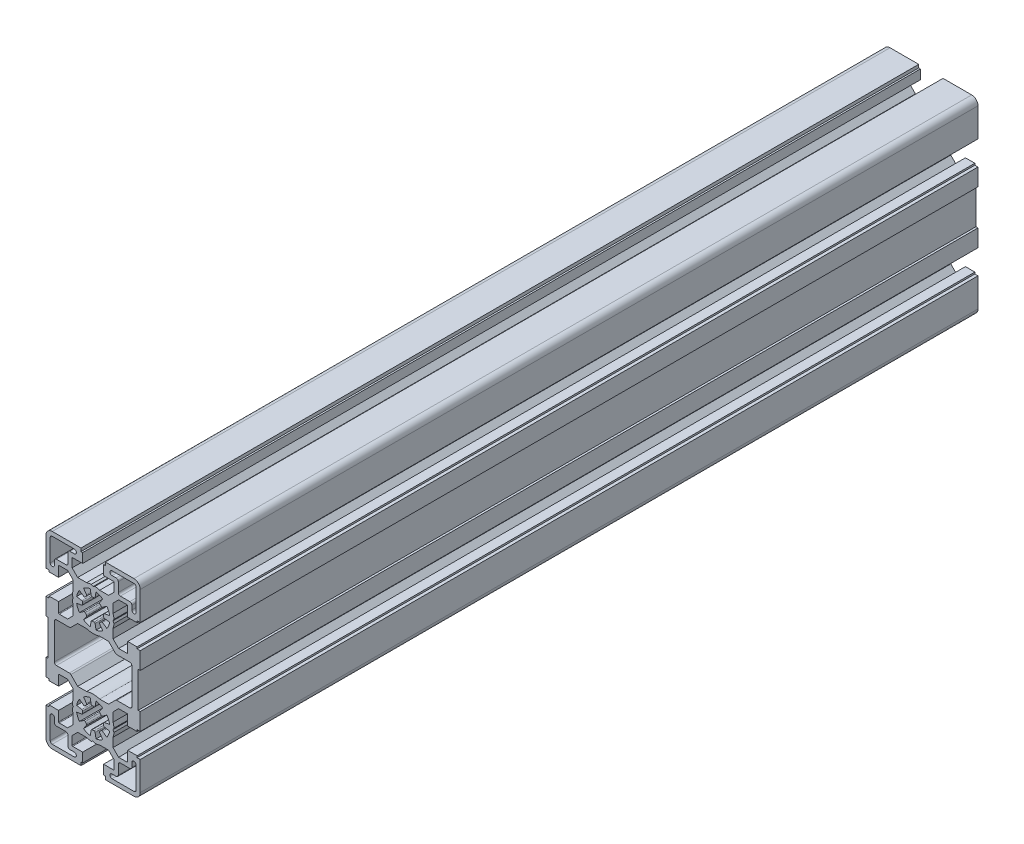
SolidWorks part; units mm, degrees
ref_plane "Спереди" through (0, 0, 0) normal (0, 0, 1) x (1, 0, 0)
ref_plane "Сверху" through (0, 0, 0) normal (0, 1, 0) x (1, 0, 0)
ref_plane "Справа" through (0, 0, 0) normal (1, 0, 0) x (0, 0, -1)
sketch "Эскиз1" plane through (0, 0, 0) normal (0, 0, 1) x (1, 0, 0)
  line L0 (-0.9511, 27.894) -> (-1.3892, 30.3785)
  line L1 (-3.1416, 26.9867) -> (-4.5886, 29.0532)
  line L2 (-4.4867, 25.6416) -> (-6.5532, 27.0886)
  line L3 (7.8785, 21.1108) -> (5.394, 21.5489)
  line L4 (-5.394, 23.4511) -> (-7.8785, 23.8892)
  line L5 (16.5, 27.5) -> (21, 27.5)
  line L6 (-21, 27.5) -> (-16.5, 27.5)
  line L7 (21, 28.3) -> (22.5, 28.3)
  line L8 (-22.5, 28.3) -> (-21, 28.3)
  line L9 (3.1225, 32) -> (7.3787, 32)
  line L10 (-7.3787, 32) -> (-3.1225, 32)
  line L11 (12.1713, 32.55) -> (16.2, 32.55)
  line L12 (-16.2, 32.55) -> (-12.1713, 32.55)
  line L13 (-17.5, 34.5) -> (-13, 34.5)
  line L14 (5, 39) -> (9.75, 39)
  line L15 (-9.75, 39) -> (-5, 39)
  line L16 (-19.5, 43) -> (-9, 43)
  line L17 (5, 43.5) -> (5.8, 43.5)
  line L18 (-5.8, 43.5) -> (-5, 43.5)
  line L19 (5.8, 45) -> (19.5, 45)
  line L20 (-19.5, 45) -> (-5.8, 45)
  line L21 (-7.8785, 21.1108) -> (-5.394, 21.5489)
  line L22 (5.394, 23.4511) -> (7.8785, 23.8892)
  line L23 (4.4867, 25.6416) -> (6.5532, 27.0886)
  line L24 (3.1416, 26.9867) -> (4.5886, 29.0532)
  line L25 (0.9511, 27.894) -> (1.3892, 30.3785)
  line L26 (-22.5, 28.3) -> (-22.5, 42)
  line L27 (-21, 27.5) -> (-21, 28.3)
  line L28 (-20.5, 31.5) -> (-20.5, 42)
  line L29 (-16.5, 27.5) -> (-16.5, 32.25)
  line L30 (-12, 35.5) -> (-12, 40)
  line L31 (-5.8, 43.5) -> (-5.8, 45)
  line L32 (-5, 39) -> (-5, 43.5)
  line L33 (5, 39) -> (5, 43.5)
  line L34 (5.8, 43.5) -> (5.8, 45)
  line L35 (9.5, 25.6225) -> (9.5, 29.8787)
  line L36 (10.05, 34.6713) -> (10.05, 38.7)
  line L37 (16.5, 27.5) -> (16.5, 32.25)
  line L38 (21, 27.5) -> (21, 28.3)
  line L39 (22.5, 28.3) -> (22.5, 42)
  line L40 (1.3892, 14.6215) -> (0.9511, 17.106)
  line L41 (4.5886, 15.9468) -> (3.1416, 18.0133)
  line L42 (6.5532, 17.9114) -> (4.4867, 19.3584)
  line L43 (-7.3787, 13) -> (-3.1225, 13)
  line L44 (3.1225, 13) -> (7.3787, 13)
  line L45 (-6.5532, 17.9114) -> (-4.4867, 19.3584)
  line L46 (-4.5886, 15.9468) -> (-3.1416, 18.0133)
  line L47 (-1.3892, 14.6215) -> (-0.9511, 17.106)
  line L48 (-9.5, 15.1213) -> (-9.5, 19.3775)
  line L49 (9.5, 15.1213) -> (9.5, 19.3775)
  line L50 (-22.5, 16.7) -> (-21, 16.7)
  line L51 (-21, 17.5) -> (-16.5, 17.5)
  line L52 (-21, 16.7) -> (-21, 17.5)
  line L53 (-16.5, 12.75) -> (-16.5, 17.5)
  line L54 (21, 16.7) -> (22.5, 16.7)
  line L55 (16.5, 17.5) -> (21, 17.5)
  line L56 (21, 16.7) -> (21, 17.5)
  line L57 (16.5, 12.75) -> (16.5, 17.5)
  line L58 (12.1713, 12.45) -> (16.2, 12.45)
  line L59 (-16.2, 12.45) -> (-12.1713, 12.45)
  line L60 (-9.5, 25.6225) -> (-9.5, 29.8787)
  line L61 (-9.5, 29.8787) -> (-12.1713, 32.55)
  line L62 (7.3787, 32) -> (10.05, 34.6713)
  line L63 (9.5, 29.8787) -> (12.1713, 32.55)
  line L64 (9.5, 15.1213) -> (12.1713, 12.45)
  line L65 (-7.3787, 13) -> (-10.6358, 9.7429)
  line L66 (-12.1713, 12.45) -> (-9.5, 15.1213)
  line L67 (-10.05, 34.6713) -> (-10.05, 38.7)
  line L68 (-10.05, 34.6713) -> (-7.3787, 32)
  line L69 (-9.4624, 22.5) -> (-9.9624, 23.366)
  line L70 (-9.4624, 22.5) -> (-9.9624, 21.634)
  line L71 (0, 31.9624) -> (0.866, 32.4624)
  line L72 (0, 31.9624) -> (-0.866, 32.4624)
  line L73 (9.4624, 22.5) -> (9.9624, 21.634)
  line L74 (9.4624, 22.5) -> (9.9624, 23.366)
  line L75 (-11, 41) -> (-9, 41)
  line L76 (-18.5, 33.5) -> (-18.5, 31.5)
  line L77 (17.5, 34.5) -> (13, 34.5)
  line L78 (12, 35.5) -> (12, 40)
  line L79 (19.5, 43) -> (9, 43)
  line L80 (11, 41) -> (9, 41)
  line L81 (20.5, 31.5) -> (20.5, 42)
  line L82 (18.5, 33.5) -> (18.5, 31.5)
  line L83 (-0.9511, -27.894) -> (-1.3892, -30.3785)
  line L84 (-3.1416, -26.9867) -> (-4.5886, -29.0532)
  line L85 (-4.4867, -25.6416) -> (-6.5532, -27.0886)
  line L86 (7.8785, -21.1108) -> (5.394, -21.5489)
  line L87 (-5.394, -23.4511) -> (-7.8785, -23.8892)
  line L88 (16.5, -27.5) -> (21, -27.5)
  line L89 (-21, -27.5) -> (-16.5, -27.5)
  line L90 (21, -28.3) -> (22.5, -28.3)
  line L91 (-22.5, -28.3) -> (-21, -28.3)
  line L92 (3.1225, -32) -> (7.3787, -32)
  line L93 (-7.3787, -32) -> (-3.1225, -32)
  line L94 (12.1713, -32.55) -> (16.2, -32.55)
  line L95 (-16.2, -32.55) -> (-12.1713, -32.55)
  line L96 (-17.5, -34.5) -> (-13, -34.5)
  line L97 (5, -39) -> (9.75, -39)
  line L98 (-9.75, -39) -> (-5, -39)
  line L99 (-19.5, -43) -> (-9, -43)
  line L100 (5, -43.5) -> (5.8, -43.5)
  line L101 (-5.8, -43.5) -> (-5, -43.5)
  line L102 (5.8, -45) -> (19.5, -45)
  line L103 (-19.5, -45) -> (-5.8, -45)
  line L104 (-7.8785, -21.1108) -> (-5.394, -21.5489)
  line L105 (5.394, -23.4511) -> (7.8785, -23.8892)
  line L106 (4.4867, -25.6416) -> (6.5532, -27.0886)
  line L107 (3.1416, -26.9867) -> (4.5886, -29.0532)
  line L108 (0.9511, -27.894) -> (1.3892, -30.3785)
  line L109 (-22.5, -28.3) -> (-22.5, -42)
  line L110 (-21, -27.5) -> (-21, -28.3)
  line L111 (-20.5, -31.5) -> (-20.5, -42)
  line L112 (-16.5, -27.5) -> (-16.5, -32.25)
  line L113 (-12, -35.5) -> (-12, -40)
  line L114 (-5.8, -43.5) -> (-5.8, -45)
  line L115 (-5, -39) -> (-5, -43.5)
  line L116 (5, -39) -> (5, -43.5)
  line L117 (5.8, -43.5) -> (5.8, -45)
  line L118 (9.5, -25.6225) -> (9.5, -29.8787)
  line L119 (10.05, -34.6713) -> (10.05, -38.7)
  line L120 (16.5, -27.5) -> (16.5, -32.25)
  line L121 (21, -27.5) -> (21, -28.3)
  line L122 (22.5, -28.3) -> (22.5, -42)
  line L123 (1.3892, -14.6215) -> (0.9511, -17.106)
  line L124 (4.5886, -15.9468) -> (3.1416, -18.0133)
  line L125 (6.5532, -17.9114) -> (4.4867, -19.3584)
  line L126 (-7.3787, -13) -> (-3.1225, -13)
  line L127 (3.1225, -13) -> (7.3787, -13)
  line L128 (-6.5532, -17.9114) -> (-4.4867, -19.3584)
  line L129 (-4.5886, -15.9468) -> (-3.1416, -18.0133)
  line L130 (-1.3892, -14.6215) -> (-0.9511, -17.106)
  line L131 (-9.5, -15.1213) -> (-9.5, -19.3775)
  line L132 (9.5, -15.1213) -> (9.5, -19.3775)
  line L133 (-22.5, -16.7) -> (-21, -16.7)
  line L134 (-21, -17.5) -> (-16.5, -17.5)
  line L135 (-21, -16.7) -> (-21, -17.5)
  line L136 (-16.5, -12.75) -> (-16.5, -17.5)
  line L137 (-22.5, 16.7) -> (-22.5, 8.5)
  line L138 (21, -16.7) -> (22.5, -16.7)
  line L139 (16.5, -17.5) -> (21, -17.5)
  line L140 (21, -16.7) -> (21, -17.5)
  line L141 (16.5, -12.75) -> (16.5, -17.5)
  line L142 (12.1713, -12.45) -> (16.2, -12.45)
  line L143 (22.5, 16.7) -> (22.5, 8.5)
  line L144 (-16.2, -12.45) -> (-12.1713, -12.45)
  line L145 (-9.5, -25.6225) -> (-9.5, -29.8787)
  line L146 (-9.5, -29.8787) -> (-12.1713, -32.55)
  line L147 (7.3787, -32) -> (10.05, -34.6713)
  line L148 (9.5, -29.8787) -> (12.1713, -32.55)
  line L149 (9.5, -15.1213) -> (12.1713, -12.45)
  line L150 (-7.3787, -13) -> (-10.6358, -9.7429)
  line L151 (-12.1713, -12.45) -> (-9.5, -15.1213)
  line L152 (-10.05, -34.6713) -> (-10.05, -38.7)
  line L153 (-10.05, -34.6713) -> (-7.3787, -32)
  line L154 (-9.4624, -22.5) -> (-9.9624, -23.366)
  line L155 (-9.4624, -22.5) -> (-9.9624, -21.634)
  line L156 (0, -31.9624) -> (0.866, -32.4624)
  line L157 (0, -31.9624) -> (-0.866, -32.4624)
  line L158 (9.4624, -22.5) -> (9.9624, -21.634)
  line L159 (9.4624, -22.5) -> (9.9624, -23.366)
  line L160 (-11, -41) -> (-9, -41)
  line L161 (-18.5, -33.5) -> (-18.5, -31.5)
  line L162 (17.5, -34.5) -> (13, -34.5)
  line L163 (12, -35.5) -> (12, -40)
  line L164 (19.5, -43) -> (9, -43)
  line L165 (11, -41) -> (9, -41)
  line L166 (20.5, -31.5) -> (20.5, -42)
  line L167 (18.5, -33.5) -> (18.5, -31.5)
  line L168 (-11.3429, -9.45) -> (-17.5, -9.45)
  line L169 (-18.5, -8.45) -> (-18.5, 8.45)
  line L170 (-11.3429, 9.45) -> (-17.5, 9.45)
  line L171 (-21.5, -8.5) -> (-21.5, 8.5)
  line L172 (-21.5, -8.5) -> (-22.5, -8.5)
  line L173 (-21.5, 8.5) -> (-22.5, 8.5)
  line L174 (21.5, -8.5) -> (21.5, 8.5)
  line L175 (21.5, -8.5) -> (22.5, -8.5)
  line L176 (21.5, 8.5) -> (22.5, 8.5)
  line L177 (-22.5, -8.5) -> (-22.5, -16.7)
  line L178 (22.5, -8.5) -> (22.5, -16.7)
  line L179 (11.3429, -9.45) -> (17.5, -9.45)
  line L180 (18.5, -8.45) -> (18.5, 8.45)
  line L181 (11.3429, 9.45) -> (17.5, 9.45)
  line L182 (7.3787, -13) -> (10.6358, -9.7429)
  line L183 (7.3787, 13) -> (10.6358, 9.7429)
  arc A0 (-19.5, 43) -> (-20.5, 42) centre (-19.5, 42) ccw
  arc A1 (-19.5, 45) -> (-22.5, 42) centre (-19.5, 42) ccw
  arc A2 (-13, 34.5) -> (-12, 35.5) centre (-13, 35.5) ccw
  arc A3 (-3.2283, 26.3181) -> (-3.8181, 25.7283) centre (0, 22.5) ccw
  arc A4 (3.8181, 25.7283) -> (3.2283, 26.3181) centre (0, 22.5) ccw
  arc A5 (-4.9826, 22.917) -> (-4.9826, 22.083) centre (0, 22.5) ccw
  arc A6 (0.417, 27.4826) -> (-0.417, 27.4826) centre (0, 22.5) ccw
  arc A7 (4.9826, 22.083) -> (4.9826, 22.917) centre (0, 22.5) ccw
  arc A8 (-6.5532, 27.0886) -> (-7.8785, 23.8892) centre (0, 22.5) ccw
  arc A9 (-1.3892, 30.3785) -> (-4.5886, 29.0532) centre (0, 22.5) ccw
  arc A10 (4.5886, 29.0532) -> (1.3892, 30.3785) centre (0, 22.5) ccw
  arc A11 (7.8785, 23.8892) -> (6.5532, 27.0886) centre (0, 22.5) ccw
  arc A12 (22.5, 42) -> (19.5, 45) centre (19.5, 42) ccw
  arc A13 (3.2283, 18.6819) -> (3.8181, 19.2717) centre (0, 22.5) ccw
  arc A14 (-3.8181, 19.2717) -> (-3.2283, 18.6819) centre (0, 22.5) ccw
  arc A15 (-0.417, 17.5174) -> (0.417, 17.5174) centre (0, 22.5) ccw
  arc A16 (6.5532, 17.9114) -> (7.8785, 21.1108) centre (0, 22.5) ccw
  arc A17 (1.3892, 14.6215) -> (4.5886, 15.9468) centre (0, 22.5) ccw
  arc A18 (-4.5886, 15.9468) -> (-1.3892, 14.6215) centre (0, 22.5) ccw
  arc A19 (-7.8785, 21.1108) -> (-6.5532, 17.9114) centre (0, 22.5) ccw
  arc A20 (-4.4867, 25.6416) -> (-3.8181, 25.7283) centre (-4.1999, 26.0512) ccw
  arc A21 (-3.2283, 26.3181) -> (-3.1416, 26.9867) centre (-3.5512, 26.6999) ccw
  arc A22 (-0.9511, 27.894) -> (-0.417, 27.4826) centre (-0.4587, 27.9808) ccw
  arc A23 (0.417, 27.4826) -> (0.9511, 27.894) centre (0.4587, 27.9808) ccw
  arc A24 (3.1416, 26.9867) -> (3.2283, 26.3181) centre (3.5512, 26.6999) ccw
  arc A25 (3.8181, 25.7283) -> (4.4867, 25.6416) centre (4.1999, 26.0512) ccw
  arc A26 (5.394, 23.4511) -> (4.9826, 22.917) centre (5.4808, 22.9587) ccw
  arc A27 (4.9826, 22.083) -> (5.394, 21.5489) centre (5.4808, 22.0413) ccw
  arc A28 (4.4867, 19.3584) -> (3.8181, 19.2717) centre (4.1999, 18.9488) ccw
  arc A29 (3.2283, 18.6819) -> (3.1416, 18.0133) centre (3.5512, 18.3001) ccw
  arc A30 (0.9511, 17.106) -> (0.417, 17.5174) centre (0.4587, 17.0192) ccw
  arc A31 (-0.417, 17.5174) -> (-0.9511, 17.106) centre (-0.4587, 17.0192) ccw
  arc A32 (-3.1416, 18.0133) -> (-3.2283, 18.6819) centre (-3.5512, 18.3001) ccw
  arc A33 (-3.8181, 19.2717) -> (-4.4867, 19.3584) centre (-4.1999, 18.9488) ccw
  arc A34 (-5.394, 21.5489) -> (-4.9826, 22.083) centre (-5.4808, 22.0413) ccw
  arc A35 (-4.9826, 22.917) -> (-5.394, 23.4511) centre (-5.4808, 22.9587) ccw
  arc A36 (-16.5, 12.75) -> (-16.2, 12.45) centre (-16.2, 12.75) ccw
  arc A37 (16.2, 12.45) -> (16.5, 12.75) centre (16.2, 12.75) ccw
  arc A38 (16.5, 32.25) -> (16.2, 32.55) centre (16.2, 32.25) ccw
  arc A39 (10.05, 38.7) -> (9.75, 39) centre (9.75, 38.7) ccw
  arc A40 (-9.75, 39) -> (-10.05, 38.7) centre (-9.75, 38.7) ccw
  arc A41 (-16.2, 32.55) -> (-16.5, 32.25) centre (-16.2, 32.25) ccw
  arc A42 (-9.9624, 21.634) -> (-9.5, 19.3775) centre (0, 22.5) ccw
  arc A43 (-9.5, 25.6225) -> (-9.9624, 23.366) centre (0, 22.5) ccw
  arc A44 (3.1225, 32) -> (0.866, 32.4624) centre (0, 22.5) ccw
  arc A45 (9.5, 19.3775) -> (9.9624, 21.634) centre (0, 22.5) ccw
  arc A46 (-0.866, 32.4624) -> (-3.1225, 32) centre (0, 22.5) ccw
  arc A47 (9.9624, 23.366) -> (9.5, 25.6225) centre (0, 22.5) ccw
  arc A48 (-11, 41) -> (-12, 40) centre (-11, 40) ccw
  arc A49 (-9, 41) -> (-9, 43) centre (-9, 42) ccw
  arc A50 (-17.5, 34.5) -> (-18.5, 33.5) centre (-17.5, 33.5) ccw
  arc A51 (-20.5, 31.5) -> (-18.5, 31.5) centre (-19.5, 31.5) ccw
  arc A52 (20.5, 42) -> (19.5, 43) centre (19.5, 42) ccw
  arc A53 (12, 35.5) -> (13, 34.5) centre (13, 35.5) ccw
  arc A54 (12, 40) -> (11, 41) centre (11, 40) ccw
  arc A55 (18.5, 33.5) -> (17.5, 34.5) centre (17.5, 33.5) ccw
  arc A56 (9, 43) -> (9, 41) centre (9, 42) ccw
  arc A57 (18.5, 31.5) -> (20.5, 31.5) centre (19.5, 31.5) ccw
  arc A58 (-20.5, -42) -> (-19.5, -43) centre (-19.5, -42) ccw
  arc A59 (-22.5, -42) -> (-19.5, -45) centre (-19.5, -42) ccw
  arc A60 (-12, -35.5) -> (-13, -34.5) centre (-13, -35.5) ccw
  arc A61 (-3.8181, -25.7283) -> (-3.2283, -26.3181) centre (0, -22.5) ccw
  arc A62 (3.2283, -26.3181) -> (3.8181, -25.7283) centre (0, -22.5) ccw
  arc A63 (-4.9826, -22.083) -> (-4.9826, -22.917) centre (0, -22.5) ccw
  arc A64 (-0.417, -27.4826) -> (0.417, -27.4826) centre (0, -22.5) ccw
  arc A65 (4.9826, -22.917) -> (4.9826, -22.083) centre (0, -22.5) ccw
  arc A66 (-7.8785, -23.8892) -> (-6.5532, -27.0886) centre (0, -22.5) ccw
  arc A67 (-4.5886, -29.0532) -> (-1.3892, -30.3785) centre (0, -22.5) ccw
  arc A68 (1.3892, -30.3785) -> (4.5886, -29.0532) centre (0, -22.5) ccw
  arc A69 (6.5532, -27.0886) -> (7.8785, -23.8892) centre (0, -22.5) ccw
  arc A70 (19.5, -45) -> (22.5, -42) centre (19.5, -42) ccw
  arc A71 (3.8181, -19.2717) -> (3.2283, -18.6819) centre (0, -22.5) ccw
  arc A72 (-3.2283, -18.6819) -> (-3.8181, -19.2717) centre (0, -22.5) ccw
  arc A73 (0.417, -17.5174) -> (-0.417, -17.5174) centre (0, -22.5) ccw
  arc A74 (7.8785, -21.1108) -> (6.5532, -17.9114) centre (0, -22.5) ccw
  arc A75 (4.5886, -15.9468) -> (1.3892, -14.6215) centre (0, -22.5) ccw
  arc A76 (-1.3892, -14.6215) -> (-4.5886, -15.9468) centre (0, -22.5) ccw
  arc A77 (-6.5532, -17.9114) -> (-7.8785, -21.1108) centre (0, -22.5) ccw
  arc A78 (-3.8181, -25.7283) -> (-4.4867, -25.6416) centre (-4.1999, -26.0512) ccw
  arc A79 (-3.1416, -26.9867) -> (-3.2283, -26.3181) centre (-3.5512, -26.6999) ccw
  arc A80 (-0.417, -27.4826) -> (-0.9511, -27.894) centre (-0.4587, -27.9808) ccw
  arc A81 (0.9511, -27.894) -> (0.417, -27.4826) centre (0.4587, -27.9808) ccw
  arc A82 (3.2283, -26.3181) -> (3.1416, -26.9867) centre (3.5512, -26.6999) ccw
  arc A83 (4.4867, -25.6416) -> (3.8181, -25.7283) centre (4.1999, -26.0512) ccw
  arc A84 (4.9826, -22.917) -> (5.394, -23.4511) centre (5.4808, -22.9587) ccw
  arc A85 (5.394, -21.5489) -> (4.9826, -22.083) centre (5.4808, -22.0413) ccw
  arc A86 (3.8181, -19.2717) -> (4.4867, -19.3584) centre (4.1999, -18.9488) ccw
  arc A87 (3.1416, -18.0133) -> (3.2283, -18.6819) centre (3.5512, -18.3001) ccw
  arc A88 (0.417, -17.5174) -> (0.9511, -17.106) centre (0.4587, -17.0192) ccw
  arc A89 (-0.9511, -17.106) -> (-0.417, -17.5174) centre (-0.4587, -17.0192) ccw
  arc A90 (-3.2283, -18.6819) -> (-3.1416, -18.0133) centre (-3.5512, -18.3001) ccw
  arc A91 (-4.4867, -19.3584) -> (-3.8181, -19.2717) centre (-4.1999, -18.9488) ccw
  arc A92 (-4.9826, -22.083) -> (-5.394, -21.5489) centre (-5.4808, -22.0413) ccw
  arc A93 (-5.394, -23.4511) -> (-4.9826, -22.917) centre (-5.4808, -22.9587) ccw
  arc A94 (-16.2, -12.45) -> (-16.5, -12.75) centre (-16.2, -12.75) ccw
  arc A95 (16.5, -12.75) -> (16.2, -12.45) centre (16.2, -12.75) ccw
  arc A96 (16.2, -32.55) -> (16.5, -32.25) centre (16.2, -32.25) ccw
  arc A97 (9.75, -39) -> (10.05, -38.7) centre (9.75, -38.7) ccw
  arc A98 (-10.05, -38.7) -> (-9.75, -39) centre (-9.75, -38.7) ccw
  arc A99 (-16.5, -32.25) -> (-16.2, -32.55) centre (-16.2, -32.25) ccw
  arc A100 (-9.5, -19.3775) -> (-9.9624, -21.634) centre (0, -22.5) ccw
  arc A101 (-9.9624, -23.366) -> (-9.5, -25.6225) centre (0, -22.5) ccw
  arc A102 (0.866, -32.4624) -> (3.1225, -32) centre (0, -22.5) ccw
  arc A103 (9.9624, -21.634) -> (9.5, -19.3775) centre (0, -22.5) ccw
  arc A104 (-3.1225, -32) -> (-0.866, -32.4624) centre (0, -22.5) ccw
  arc A105 (9.5, -25.6225) -> (9.9624, -23.366) centre (0, -22.5) ccw
  arc A106 (-12, -40) -> (-11, -41) centre (-11, -40) ccw
  arc A107 (-9, -43) -> (-9, -41) centre (-9, -42) ccw
  arc A108 (-18.5, -33.5) -> (-17.5, -34.5) centre (-17.5, -33.5) ccw
  arc A109 (-18.5, -31.5) -> (-20.5, -31.5) centre (-19.5, -31.5) ccw
  arc A110 (19.5, -43) -> (20.5, -42) centre (19.5, -42) ccw
  arc A111 (13, -34.5) -> (12, -35.5) centre (13, -35.5) ccw
  arc A112 (11, -41) -> (12, -40) centre (11, -40) ccw
  arc A113 (17.5, -34.5) -> (18.5, -33.5) centre (17.5, -33.5) ccw
  arc A114 (9, -41) -> (9, -43) centre (9, -42) ccw
  arc A115 (20.5, -31.5) -> (18.5, -31.5) centre (19.5, -31.5) ccw
  arc A116 (-3.1225, 13) -> (3.1225, 13) centre (0, 22.5) ccw
  arc A117 (3.1225, -13) -> (-3.1225, -13) centre (0, -22.5) ccw
  arc A118 (-17.5, 9.45) -> (-18.5, 8.45) centre (-17.5, 8.45) ccw
  arc A119 (-18.5, -8.45) -> (-17.5, -9.45) centre (-17.5, -8.45) ccw
  arc A120 (-11.3429, 9.45) -> (-10.6358, 9.7429) centre (-11.3429, 10.45) ccw
  arc A121 (-10.6358, -9.7429) -> (-11.3429, -9.45) centre (-11.3429, -10.45) ccw
  arc A122 (18.5, 8.45) -> (17.5, 9.45) centre (17.5, 8.45) ccw
  arc A123 (17.5, -9.45) -> (18.5, -8.45) centre (17.5, -8.45) ccw
  arc A124 (10.6358, 9.7429) -> (11.3429, 9.45) centre (11.3429, 10.45) ccw
  arc A125 (11.3429, -9.45) -> (10.6358, -9.7429) centre (11.3429, -10.45) ccw
extrude "Бобышка-Вытянуть1" add sketch "Эскиз1" along normal blind 400
